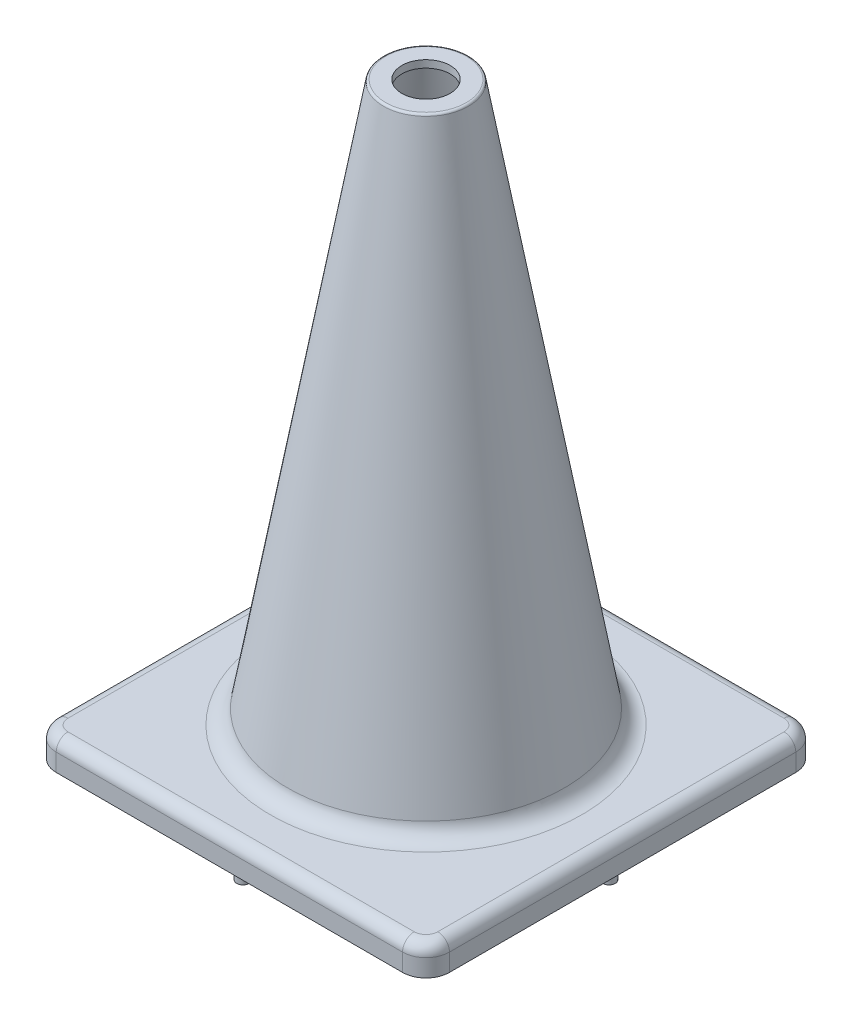
SolidWorks part; units mm, degrees
ref_plane "Front Plane" through (0, 0, 0) normal (0, 0, 1) x (1, 0, 0)
ref_plane "Top Plane" through (0, 0, 0) normal (0, 1, 0) x (1, 0, 0)
ref_plane "Right Plane" through (0, 0, 0) normal (1, 0, 0) x (0, 0, -1)
sketch "Sketch1" plane through (0, 0, 0) normal (0, 1, 0) x (1, 0, 0)
  line L1 (-93.6625, -106.3625) -> (93.6625, -106.3625)
  line L2 (-106.3625, -93.6625) -> (-106.3625, 93.6625)
  line L3 (-93.6625, 106.3625) -> (93.6625, 106.3625)
  line L4 (106.3625, -93.6625) -> (106.3625, 93.6625)
  line L5 (-106.3625, -106.3625) -> (106.3625, 106.3625) construction
  line L6 (-106.3625, 106.3625) -> (106.3625, -106.3625) construction
  arc A0 (-93.6625, -106.3625) -> (-106.3625, -93.6625) centre (-93.6625, -93.6625) cw
  arc A1 (93.6625, -106.3625) -> (106.3625, -93.6625) centre (93.6625, -93.6625) ccw
  arc A2 (93.6625, 106.3625) -> (106.3625, 93.6625) centre (93.6625, 93.6625) cw
  arc A3 (-106.3625, 93.6625) -> (-93.6625, 106.3625) centre (-93.6625, 93.6625) cw
  point P0 (0, 0)
  dimension "D2" = 12.7
  dimension "D1" = 212.725
extrude "Boss-Extrude1" add sketch "Sketch1" along normal blind 15.875
fillet "Fillet1" radius 6.35 8 edges at (-102.6428, 15.875, 102.6428) (-106.3625, 15.875, 0) (-102.6428, 15.875, -102.6428) (0, 15.875, -106.3625) (102.6428, 15.875, -102.6428) (106.3625, 15.875, 0) (102.6428, 15.875, 102.6428) (0, 15.875, 106.3625)
sketch "Sketch2" plane through (0, 0, 0) normal (0, -1, 0) x (1, 0, 0)
  line L0 (-102.3938, 95.0973) -> (-95.0973, 102.3938)
  line L1 (-95.0973, 102.3938) -> (95.0973, 102.3938)
  line L2 (95.0973, 102.3938) -> (102.3938, 95.0973)
  line L3 (102.3938, 95.0973) -> (102.3938, -95.0973)
  line L4 (102.3938, -95.0973) -> (95.0973, -102.3937)
  line L5 (95.0973, -102.3937) -> (-95.0973, -102.3937)
  line L6 (-95.0973, -102.3937) -> (-102.3938, -95.0973)
  line L7 (-102.3938, -95.0973) -> (-102.3938, 95.0973)
  line L8 (-93.6625, 106.3625) -> (93.6625, 106.3625) construction
  line L9 (106.3625, 93.6625) -> (106.3625, -93.6625) construction
  line L10 (93.6625, -106.3625) -> (-93.6625, -106.3625) construction
  line L11 (-106.3625, -93.6625) -> (-106.3625, 93.6625) construction
  dimension "D1" = 3.9688
  dimension "D2" = 3.9688
  dimension "D3" = 3.9688
  dimension "D4" = 3.9687
  dimension "D5" = 10.3187
  dimension "D6" = 135
extrude "Cut-Extrude1" cut sketch "Sketch2" against normal blind 11.9062
sketch "Sketch3" plane through (0, 11.9062, 0) normal (0, -1, 0) x (1, 0, 0)
  line L0 (-3.3734, 102.3938) -> (-3.3734, 86.7172)
  line L1 (95.0973, 102.3938) -> (-95.0973, 102.3938) construction
  line L2 (3.3734, 102.3938) -> (3.3734, 86.7172)
  line L3 (95.0973, 102.3938) -> (-95.0973, 102.3938) construction
  line L4 (-3.3734, 102.3938) -> (3.3734, 102.3938)
  line L5 (102.3938, -3.3734) -> (86.7172, -3.3734)
  line L6 (102.3938, 3.3734) -> (86.7172, 3.3734)
  line L7 (102.3938, 3.3734) -> (102.3938, -3.3734)
  line L8 (-3.3734, -102.3938) -> (-3.3734, -86.7172)
  line L9 (3.3734, -102.3938) -> (3.3734, -86.7172)
  line L10 (3.3734, -102.3938) -> (-3.3734, -102.3938)
  line L11 (-102.3937, 3.3734) -> (-86.7172, 3.3734)
  line L12 (-102.3937, -3.3734) -> (-86.7172, -3.3734)
  line L13 (-102.3937, -3.3734) -> (-102.3937, 3.3734)
  arc A0 (-3.3734, 86.7172) -> (3.3734, 86.7172) centre (0, 86.7172) ccw
  arc A1 (86.7172, 3.3734) -> (86.7172, -3.3734) centre (86.7172, 0) ccw
  arc A2 (3.3734, -86.7172) -> (-3.3734, -86.7172) centre (0, -86.7172) ccw
  arc A3 (-86.7172, -3.3734) -> (-86.7172, 3.3734) centre (-86.7172, 0) ccw
  point P7 (0, 83.3438)
  point P29 (0, 0)
  dimension "D1" = 6.7469
  dimension "D2" = 19.05
  dimension "D3" = 4
extrude "Boss-Extrude2" add sketch "Sketch3" along normal blind 11.9062
ref_plane "Plane1" through (0, -7.1438, 0) normal (0, -1, 0) x (-1, 0, 0)
sketch "Sketch4" plane through (0, -7.1438, 0) normal (0, -1, 0) x (-1, 0, 0)
  line L0 (-3.3734, 102.3938) -> (-95.0973, 102.3937) construction
  line L1 (-3.3734, 102.3938) -> (-95.0973, 102.3937)
  line L2 (0, 86.7172) -> (0, 99.0203) construction
  line L3 (-3.3734, 86.7172) -> (-3.3734, 99.0203)
  line L4 (3.3734, 86.7172) -> (3.3734, 99.0203)
  line L5 (-92.4313, 92.4313) -> (-61.281, 61.281) construction
  line L6 (-90.0459, 94.8167) -> (-58.8956, 63.6664)
  line L7 (-94.8167, 90.0459) -> (-63.6664, 58.8956)
  line L8 (-95.0973, 102.3937) -> (-102.3938, 95.0973) construction
  line L9 (86.7172, 0) -> (99.0203, 0) construction
  line L10 (86.7172, 3.3734) -> (99.0203, 3.3734)
  line L11 (86.7172, -3.3734) -> (99.0203, -3.3734)
  line L12 (92.4313, 92.4313) -> (61.281, 61.281) construction
  line L13 (94.8167, 90.0459) -> (63.6664, 58.8956)
  line L14 (90.0459, 94.8167) -> (58.8956, 63.6664)
  line L15 (0, -86.7172) -> (0, -99.0203) construction
  line L16 (3.3734, -86.7172) -> (3.3734, -99.0203)
  line L17 (-3.3734, -86.7172) -> (-3.3734, -99.0203)
  line L18 (92.4313, -92.4313) -> (61.281, -61.281) construction
  line L19 (90.0459, -94.8167) -> (58.8956, -63.6664)
  line L20 (94.8167, -90.0459) -> (63.6664, -58.8956)
  line L21 (-86.7172, 0) -> (-99.0203, 0) construction
  line L22 (-86.7172, -3.3734) -> (-99.0203, -3.3734)
  line L23 (-86.7172, 3.3734) -> (-99.0203, 3.3734)
  line L24 (-92.4313, -92.4313) -> (-61.281, -61.281) construction
  line L25 (-94.8167, -90.0459) -> (-63.6664, -58.8956)
  line L26 (-90.0459, -94.8167) -> (-58.8956, -63.6664)
  arc A0 (-3.3734, 86.7172) -> (3.3734, 86.7172) centre (0, 86.7172) ccw construction
  arc A1 (-3.3734, 86.7172) -> (3.3734, 86.7172) centre (0, 86.7172) ccw
  arc A2 (-3.3734, 86.7172) -> (3.3734, 86.7172) centre (0, 86.7172) ccw
  arc A3 (3.3734, 99.0203) -> (-3.3734, 99.0203) centre (0, 99.0203) ccw
  arc A4 (-90.0459, 94.8167) -> (-94.8167, 90.0459) centre (-92.4313, 92.4313) ccw
  arc A5 (-63.6664, 58.8956) -> (-58.8956, 63.6664) centre (-61.281, 61.281) ccw
  arc A6 (86.7172, 3.3734) -> (86.7172, -3.3734) centre (86.7172, 0) ccw
  arc A7 (99.0203, -3.3734) -> (99.0203, 3.3734) centre (99.0203, 0) ccw
  arc A8 (94.8167, 90.0459) -> (90.0459, 94.8167) centre (92.4313, 92.4313) ccw
  arc A9 (58.8956, 63.6664) -> (63.6664, 58.8956) centre (61.281, 61.281) ccw
  arc A10 (3.3734, -86.7172) -> (-3.3734, -86.7172) centre (0, -86.7172) ccw
  arc A11 (-3.3734, -99.0203) -> (3.3734, -99.0203) centre (0, -99.0203) ccw
  arc A12 (90.0459, -94.8167) -> (94.8167, -90.0459) centre (92.4313, -92.4313) ccw
  arc A13 (63.6664, -58.8956) -> (58.8956, -63.6664) centre (61.281, -61.281) ccw
  arc A14 (-86.7172, -3.3734) -> (-86.7172, 3.3734) centre (-86.7172, 0) ccw
  arc A15 (-99.0203, 3.3734) -> (-99.0203, -3.3734) centre (-99.0203, 0) ccw
  arc A16 (-94.8167, -90.0459) -> (-90.0459, -94.8167) centre (-92.4313, -92.4313) ccw
  arc A17 (-58.8956, -63.6664) -> (-63.6664, -58.8956) centre (-61.281, -61.281) ccw
  point P7 (0, 92.8688)
  point P14 (-76.8561, 76.8561)
  point P19 (-98.7455, 98.7455)
  point P20 (-94.8167, 94.8167)
  point P23 (-58.8956, 58.8956)
  point P29 (92.8688, 0)
  point P36 (76.8561, 76.8561)
  point P43 (0, -92.8687)
  point P50 (76.8561, -76.8561)
  point P57 (-92.8687, 0)
  point P64 (-76.8561, -76.8561)
  point P69 (0, 0)
  dimension "D1" = 45
  dimension "D2" = 6.7469
  dimension "D3" = 5.5562
  dimension "D4" = 50.8
  dimension "D5" = 4
extrude "Boss-Extrude3" add sketch "Sketch4" against normal up to next contours L7 A5 L6 A4 | L4 A3 L3 A1 | L14 A9 L13 A8 | L11 A7 L10 A6 | L20 A13 L19 A12 | L17 A11 L16 A10 | L26 A17 L25 A16 | L23 A15 L22 A14
fillet "Fillet2" radius 4.7625 12 edges at (102.3938, 11.9062, -49.2354) (102.3938, 11.9062, 49.2354) (98.7455, 11.9062, 98.7455) (49.2354, 11.9062, 102.3938) (-49.2354, 11.9062, 102.3938) (-98.7455, 11.9062, 98.7455) (-102.3938, 11.9062, 49.2354) (-102.3938, 11.9062, -49.2354) (-98.7455, 11.9062, -98.7455) (-49.2354, 11.9062, -102.3937) (49.2354, 11.9062, -102.3937) (98.7455, 11.9062, -98.7455)
sketch "Sketch5" plane through (0, 0, 0) normal (0, 0, 1) x (1, 0, 0)
  line L0 (-93.6625, 15.875) -> (93.6625, 15.875) construction
  line L1 (84.1913, 15.875) -> (93.6625, 15.875)
  line L2 (74.8113, 23.7447) -> (23.0188, 317.2445)
  line L3 (21.7681, 318.2937) -> (13.0969, 318.2937)
  line L4 (13.0969, 318.2937) -> (13.0969, 314.325)
  line L5 (13.0969, 314.325) -> (19.5039, 314.325)
  line L6 (19.5039, 314.325) -> (72.1699, 15.875)
  line L7 (74.8113, 23.7447) -> (76.2, 15.875) construction
  line L8 (90.0459, -7.1438) -> (58.8956, -7.1438) construction
  line L9 (0, 0) -> (0, 318.2937) construction
  line L10 (84.1913, 15.875) -> (72.1699, 15.875)
  arc A0 (84.1913, 15.875) -> (74.8113, 23.7447) centre (84.1913, 25.4) cw
  arc A1 (23.0188, 317.2445) -> (21.7681, 318.2937) centre (21.7681, 317.0238) ccw
  dimension "D1" = 9.525
  dimension "D7" = 1.27
  dimension "D2" = 76.2
  dimension "D3" = 3.9688
  dimension "D4" = 3.9688
  dimension "D5" = 13.0969
  dimension "D6" = 325.4375
  dimension "D8" = 23.0188
revolve "Revolve1" add sketch "Sketch5" angle 360 about L9
sketch "Sketch6" plane through (0, 0, 0) normal (0, 0, 1) x (1, 0, 0)
  line L0 (74.8113, 23.7447) -> (23.0188, 317.2445) construction
  line L1 (90.0459, -7.1438) -> (58.8956, -7.1438) construction
  line L2 (0, 21.1215) -> (71.2441, 21.1215)
  line L3 (74.8113, 23.7447) -> (23.0188, 317.2445)
  line L5 (71.4815, 19.776) -> (72.8703, 11.9062) construction
  line L6 (71.4815, 19.776) -> (71.2441, 21.1215)
  line L7 (80.8616, 11.9062) -> (0, 11.9062)
  line L8 (0, 11.9062) -> (0, 21.1215)
  line L9 (0, 21.1215) -> (71.2441, 21.1215)
  arc A0 (71.4815, 19.776) -> (80.8616, 11.9062) centre (80.8616, 21.4312) ccw
  dimension "D2" = 3.9688
  dimension "D4" = 9.525
  dimension "D3" = 9.2152
  dimension "D1" = 28.2652
revolve "Cut-Revolve1" cut sketch "Sketch6" angle 360 about L8
